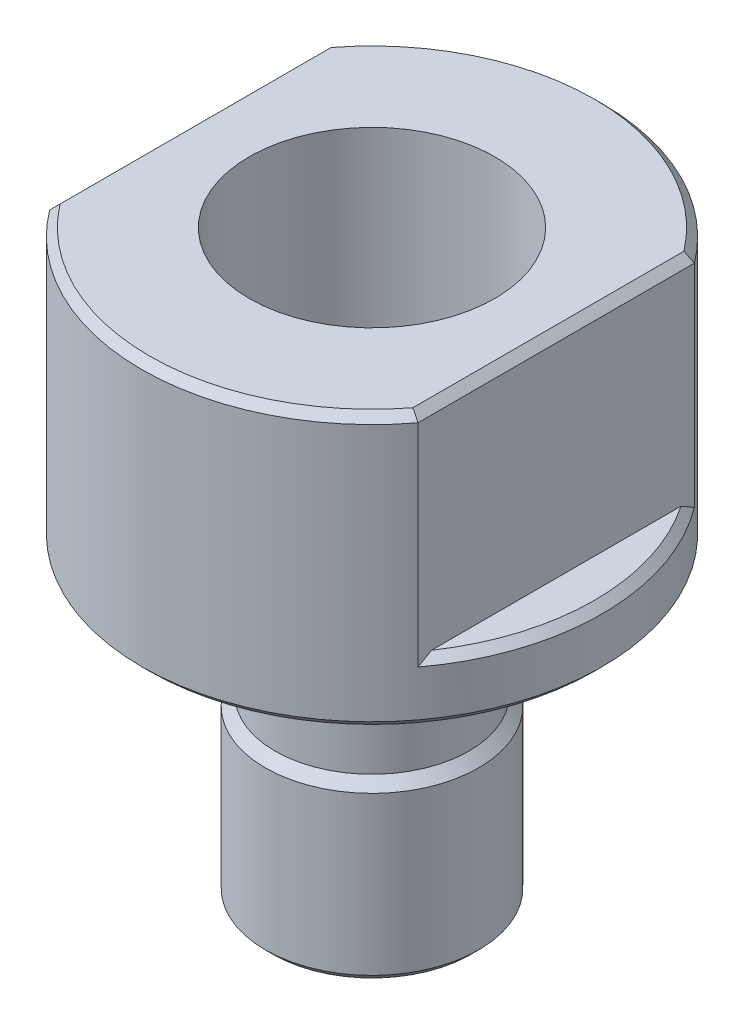
SolidWorks part; units mm, degrees
ref_plane "Front Plane" through (0, 0, 0) normal (0, 0, 1) x (1, 0, 0)
ref_plane "Top Plane" through (0, 0, 0) normal (0, 1, 0) x (1, 0, 0)
ref_plane "Right Plane" through (0, 0, 0) normal (1, 0, 0) x (0, 0, -1)
sketch "Sketch1" plane through (0, 0, 0) normal (0, 0, 1) x (1, 0, 0)
  line L0 (0, 0) -> (0, -16.7273) construction
  line L1 (7.5, 0) -> (7.5, -8.89)
  line L2 (7.5, -8.89) -> (3.475, -8.89)
  line L3 (3.475, -8.89) -> (3.475, -10.89)
  line L4 (3.475, -18.89) -> (2.0381, -18.89)
  line L5 (2.0381, -18.89) -> (2.0381, -8.0269)
  line L6 (4, 0) -> (7.5, 0)
  line L7 (3.475, -10.89) -> (3.1591, -11.2059)
  line L8 (4, -6.89) -> (4, 0)
  line L9 (4, -6.89) -> (3.175, -6.89)
  line L10 (3.1591, -11.2059) -> (3.1591, -13.1859)
  line L11 (2.0381, -8.0269) -> (3.175, -6.89)
  line L12 (3.1591, -13.1859) -> (3.475, -13.5017)
  line L13 (3.475, -13.5017) -> (3.475, -18.89)
  dimension "D1" = 15
  dimension "D2" = 6.95
  dimension "D3" = 4.0762
  dimension "D4" = 8
  dimension "D5" = 8.89
  dimension "D6" = 2
  dimension "D7" = 10
  dimension "D8" = 6.35
  dimension "D9" = 45
  dimension "D10" = 45
  dimension "D11" = 45
  dimension "D12" = 2
  dimension "D13" = 1.98
revolve "Revolve1" add sketch "Sketch1" angle 360 about L0
sketch "Sketch2" plane through (0, 0, 0) normal (0, 1, 0) x (1, 0, 0)
  line L1 (6, -10.2767) -> (-6, -10.2767)
  line L2 (6, -10.2767) -> (6, 10.2767)
  line L3 (6, 10.2767) -> (-6, 10.2767)
  line L4 (-6, -10.2767) -> (-6, 10.2767)
  line L5 (6, -10.2767) -> (-6, 10.2767) construction
  line L6 (6, 10.2767) -> (-6, -10.2767) construction
  line L7 (10.0674, -14.7139) -> (-10.0674, -14.7139)
  line L8 (10.0674, -14.7139) -> (10.0674, 14.7139)
  line L9 (10.0674, 14.7139) -> (-10.0674, 14.7139)
  line L10 (-10.0674, -14.7139) -> (-10.0674, 14.7139)
  line L11 (10.0674, -14.7139) -> (-10.0674, 14.7139) construction
  line L12 (10.0674, 14.7139) -> (-10.0674, -14.7139) construction
  point P0 (0, 0)
  point P6 (0, 0)
  dimension "D1" = 12
extrude "Cut-Extrude1" cut sketch "Sketch2" against normal offset from surface (6.89 mm away) 2 up to face at (0, -8.89, 7.5)
chamfer "Chamfer3" [suppressed] distance 1.5 angle 45
chamfer "Chamfer2" distance 0.254 angle 45 2 edges at (0, -8.89, 7.5) (0, -18.89, 3.475)
chamfer "Chamfer4" distance 0.254 angle 45 4 edges at (-6, 0, 0) (0, 0, -7.5) (0, 0, 7.5) (6, 0, 0)
chamfer "Chamfer5" distance 0.254 angle 45 2 edges at (-7.5, -6.89, 0) (7.5, -6.89, 0)
